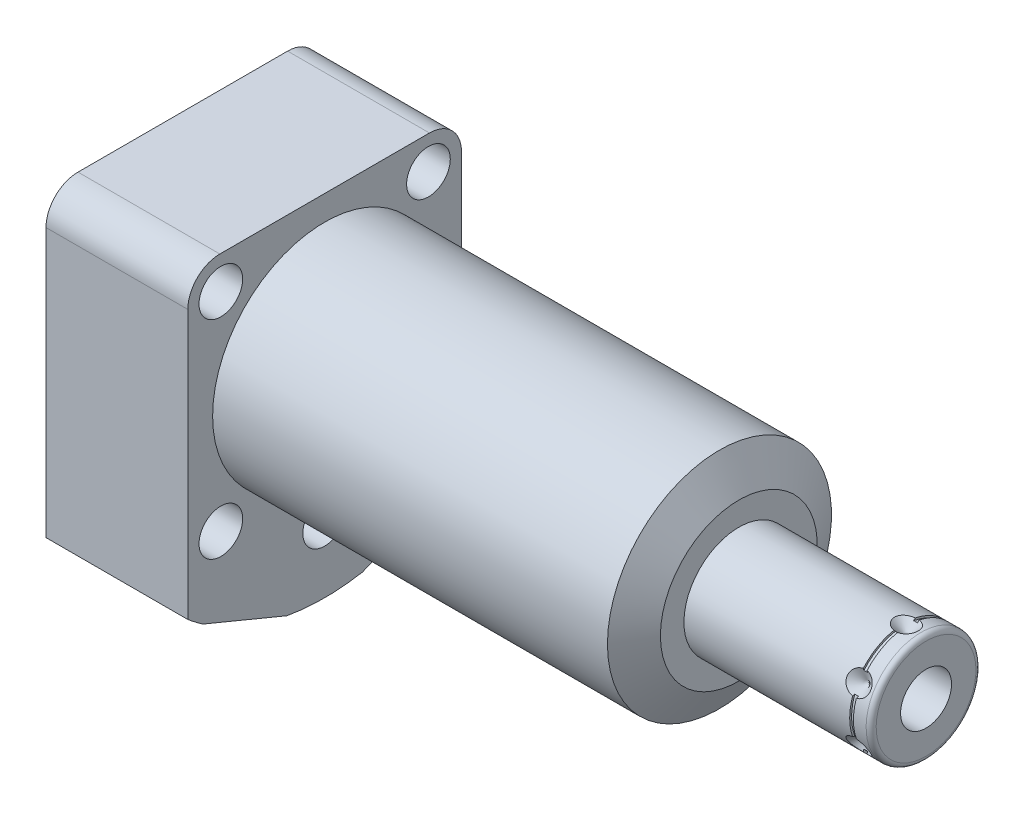
SolidWorks part; units mm, degrees
material "Alloy Steel"
ref_plane "Front Plane" through (0, 0, 0) normal (0, 0, 1) x (1, 0, 0)
ref_plane "Top Plane" through (0, 0, 0) normal (0, 1, 0) x (1, 0, 0)
ref_plane "Right Plane" through (0, 0, 0) normal (1, 0, 0) x (0, 0, -1)
sketch "Sketch1" plane through (0, 0, 0) normal (1, 0, 0) x (0, 0, -1)
  line L0 (-27.686, 27.686) -> (-27.686, -33.136)
  line L1 (-24.6412, -35.4588) -> (-7.6492, -42.4971)
  line L2 (7.6492, -42.4971) -> (24.6412, -35.4588)
  line L3 (27.686, -33.136) -> (27.686, 27.686)
  line L4 (27.686, 27.686) -> (-27.686, 27.686)
  line L5 (0, -34.1122) -> (0, 17.8562) construction
  line L6 (-36.4519, 0) -> (54.4719, 0) construction
  arc A0 (-7.6492, -42.4971) -> (7.6492, -42.4971) centre (0, 0) ccw
  arc A1 (-27.686, -33.136) -> (-24.6412, -35.4588) centre (0, 0) ccw
  arc A2 (24.6412, -35.4588) -> (27.686, -33.136) centre (0, 0) ccw
  dimension "D6" = 43.18
  dimension "D1" = 55.372
  dimension "D2" = 42.1894
  dimension "D4" = 27.686
  dimension "D5" = 22.5
extrude "Extrude1" add sketch "Sketch1" along normal blind 83.82 and the other way blind 28.702
sketch "Sketch2" plane through (0, 0, 0) normal (1, 0, 0) x (0, 0, -1)
  line L6 (27.686, 27.686) -> (-27.686, 27.686)
  line L7 (-27.686, 27.686) -> (-27.686, -33.136)
  line L8 (-24.6412, -35.4588) -> (-7.6492, -42.4971)
  line L9 (7.6492, -42.4971) -> (24.6412, -35.4588)
  line L10 (27.686, -33.136) -> (27.686, 27.686)
  line L11 (27.686, 27.686) -> (-27.686, 27.686)
  line L12 (-27.686, 27.686) -> (-27.686, -33.136)
  line L13 (-24.6412, -35.4588) -> (-7.6492, -42.4971)
  line L14 (7.6492, -42.4971) -> (24.6412, -35.4588)
  line L15 (27.686, -33.136) -> (27.686, 27.686)
  circle A0 centre (0, 0) radius 22.6695
  arc A4 (-27.686, -33.136) -> (-24.6412, -35.4588) centre (0, 0) ccw
  arc A5 (-7.6492, -42.4971) -> (7.6492, -42.4971) centre (0, 0) ccw
  arc A6 (24.6412, -35.4588) -> (27.686, -33.136) centre (0, 0) ccw
  arc A7 (-27.686, -33.136) -> (-24.6412, -35.4588) centre (0, 0) ccw
  arc A8 (-7.6492, -42.4971) -> (7.6492, -42.4971) centre (0, 0) ccw
  arc A9 (24.6412, -35.4588) -> (27.686, -33.136) centre (0, 0) ccw
  dimension "D2" = 45.339
  dimension "D1" = 0
extrude "Cut-Extrude1" cut sketch "Sketch2" along normal up to next
sketch "Sketch3" plane through (0, 0, 0) normal (0, 0, 1) x (1, 0, 0)
  line L0 (79.8972, 22.6695) -> (83.82, 15.875)
  line L1 (23.3045, 0) -> (44.9603, 0) construction
  line L2 (83.82, 22.6695) -> (83.82, 15.875)
  line L3 (83.82, 22.6695) -> (79.8972, 22.6695)
  line L4 (83.82, -22.6695) -> (83.82, 22.6695) construction
  line L5 (83.82, 22.6695) -> (0, 22.6695) construction
  dimension "D1" = 30
  dimension "D2" = 31.75
revolve "Cut-Revolve1" cut sketch "Sketch3" angle 360 about L1
ref_plane "Plane19" through (0, 0, 11.8618) normal (0, 0, 1) x (1, 0, 0)
sketch "S2D0002" plane through (-24.9936, -18.1864, 11.8618) normal (0, 0, 1) x (0, 1, 0)
  line L0 (-7.1374, 2.2606) -> (-4.6863, 2.2606)
  line L1 (-7.1374, 2.2606) -> (-7.1374, -0.7366)
  line L2 (-7.1374, -0.7366) -> (-9.144, -0.7366)
  line L3 (-9.144, -0.7366) -> (-9.144, -9.7282)
  line L4 (-9.144, -9.7282) -> (-10.3886, -9.7282)
  line L5 (-10.3886, -9.7282) -> (-10.3886, 3.7084)
  line L6 (-10.3886, -23.5585) -> (-10.3886, 0.5994) construction
  line L7 (-4.6863, 2.2606) -> (-4.6863, 3.7084)
  line L8 (45.8724, 3.7084) -> (-14.9496, 3.7084) construction
  line L9 (-4.6863, 3.7084) -> (-10.3886, 3.7084)
  dimension "D1" = 1.4478
  dimension "D2" = 28.575
  dimension "D3" = 11.4046
  dimension "D4" = 6.5024
  dimension "D5" = 2.4892
  dimension "D6" = 8.9916
  dimension "D7" = 2.9972
revolve "Cut-Revolve2" cut sketch "S2D0002" angle 360 about L6
ref_plane "Plane20" through (-12.192, 0, 0) normal (1, 0, 0) x (0, 0, -1)
sketch "Sketch6" plane through (-12.192, 0, 0) normal (1, 0, 0) x (0, 0, -1)
  line L0 (-22.1962, -36.1966) -> (-25.9797, -34.6294)
  line L1 (-22.1962, -36.1966) -> (-22.1476, -36.0792)
  line L2 (-22.1476, -36.0792) -> (-21.2184, -35.6943)
  line L3 (-21.2184, -35.6943) -> (-16.1153, -23.3744)
  line L4 (-16.1153, -23.3744) -> (-10.6241, -25.6489)
  line L5 (-10.6241, -25.6489) -> (-16.1452, -38.9779)
  line L6 (-4.9702, -11.9991) -> (2.3899, 5.7696) construction
  line L7 (-25.9797, -34.6294) -> (-26.0769, -34.8641)
  line L8 (-24.6412, -35.4588) -> (-7.6492, -42.4971) construction
  line L9 (-26.0769, -34.8641) -> (-16.1452, -38.9779)
  line L10 (-24.6412, -35.4588) -> (-7.6492, -42.4971) construction
  dimension "D1" = 0.254
  dimension "D2" = 21.5
  dimension "D3" = 45
  dimension "D5" = 13.3096
  dimension "D6" = 11.8872
  dimension "D7" = 14.1732
  dimension "D8" = 0.127
revolve "Cut-Revolve4" cut sketch "Sketch6" angle 360 about L6
mirror "Mirror1" about plane through (0, 0, 0) normal (0, 0, 1) of "Cut-Revolve2", "Cut-Revolve4"
sketch "Sketch7" plane through (0, 0, 0) normal (0, 0, 1) x (1, 0, 0)
  line L0 (83.82, 0) -> (83.82, 11.1125)
  line L1 (83.82, 11.1125) -> (120.688, 11.1125)
  line L2 (121.704, 10.0965) -> (121.704, 0)
  line L3 (121.704, 0) -> (83.82, 0)
  line L4 (4.9931, 0) -> (66.1154, 0) construction
  line L5 (83.82, -15.875) -> (83.82, 15.875) construction
  line L6 (-28.702, 27.686) -> (-28.702, -33.136) construction
  arc A0 (121.704, 10.0965) -> (120.688, 11.1125) centre (120.688, 10.0965) ccw
  point P0 (83.82, 0)
  dimension "D3" = 1.016
  dimension "D1" = 150.406
  dimension "D2" = 22.225
revolve "Revolve1" add sketch "Sketch7" angle 360 about L4
sketch "S2D0001" plane through (0, 0, 0) normal (0, 0, 1) x (1, 0, 0)
  line L0 (121.704, -5.1562) -> (104.686, -5.1562)
  line L1 (104.686, -5.1562) -> (101.5878, 0)
  line L2 (121.704, -5.1562) -> (121.704, 0)
  line L3 (121.704, 0) -> (101.5878, 0)
  line L4 (-2.5273, 0) -> (-28.8062, 0) construction
  line L5 (121.704, -10.0965) -> (121.704, 10.0965) construction
  dimension "D1" = 10.3124
  dimension "D2" = 17.018
  dimension "D3" = 59
revolve "Cut-Revolve8" cut sketch "S2D0001" angle 360 about L4
sketch "Sketch9" plane through (0, 0, 0) normal (0, 0, 1) x (1, 0, 0)
  line L0 (117.7416, -11.1125) -> (115.3286, -11.1125)
  line L1 (115.3286, -11.1125) -> (117.7416, -8.6995)
  line L2 (117.7416, -11.1125) -> (117.7416, -8.6995)
  line L3 (117.7416, -6.2534) -> (117.7416, 0.0794) construction
  line L4 (83.82, -11.1125) -> (120.688, -11.1125) construction
  line L5 (121.704, -10.0965) -> (121.704, 10.0965) construction
  dimension "D1" = 3.9624
  dimension "D2" = 45
  dimension "D3" = 4.826
revolve "Cut-Revolve9" cut sketch "Sketch9" angle 360 about L3
sketch "Sketch11" plane through (0, 0, 0) normal (0, 1, 0) x (1, 0, 0)
  line L0 (118.1226, -11.1125) -> (118.1226, -10.7315)
  line L1 (118.1226, -10.7315) -> (117.3606, -10.7315)
  line L2 (117.3606, -10.7315) -> (117.3606, -11.1125)
  line L3 (117.3606, -11.1125) -> (118.1226, -11.1125)
  line L4 (0, 0) -> (83.4312, 0) construction
  line L6 (83.82, -11.1125) -> (120.688, -11.1125) construction
  line L7 (117.7416, 0) -> (117.7416, -20.2865) construction
  dimension "D1" = 0.762
  dimension "D2" = 0.381
revolve "Cut-Revolve5" cut sketch "Sketch11" angle 360 about L4
sketch "Sketch15" plane through (-24.257, 0, 0) normal (-1, 0, 0) x (0, 0, 1)
  circle A0 centre (11.8618, -28.575) radius 2.7432
  circle A1 centre (11.8618, -28.575) radius 3.2512 construction
  dimension "D1" = 5.4864
extrude "Extrude3" add sketch "Sketch15" along normal blind 2.9972
sketch "Sketch16" plane through (-27.2542, 0, 0) normal (-1, 0, 0) x (0, 0, 1)
  line L7 (13.2989, -28.575) -> (12.5804, -27.3304)
  line L8 (12.5804, -27.3304) -> (11.1432, -27.3304)
  line L9 (11.1432, -27.3304) -> (10.4247, -28.575)
  line L10 (10.4247, -28.575) -> (11.1432, -29.8196)
  line L11 (11.1432, -29.8196) -> (12.5804, -29.8196)
  line L12 (12.5804, -29.8196) -> (13.2989, -28.575)
  circle A0 centre (11.8618, -28.575) radius 1.2446 construction
  dimension "D1" = 2.4892
extrude "Cut-Extrude2" cut sketch "Sketch16" against normal blind 2.54
chamfer "Chamfer1" distance 0.381 angle 45 1 edges at (-27.2542, -28.575, 14.605)
mirror "Mirror2" about plane through (0, 0, 0) normal (0, 0, 1) of "Extrude3", "Cut-Extrude2", "Chamfer1"
sketch "Sketch21" plane through (0, 0, 11.8618) normal (0, 0, 1) x (1, 0, 0)
  line L0 (-35.9744, -28.575) -> (-17.6399, -28.575) construction
  line L3 (-27.2542, -22.8727) -> (-27.2542, -34.2773) construction
  line L4 (-24.257, -28.575) -> (-18.0186, -28.575) construction
  circle A0 centre (-28.1178, -23.7617) radius 0.889
  dimension "D1" = 1.778
  dimension "D2" = 9.6266
  dimension "D3" = 0.8636
revolve "Revolve4" add sketch "Sketch21" angle 360 about L0
mirror "Mirror3" about plane through (0, 0, 0) normal (0, 0, 1) of bodies 129
fillet "Fillet1" radius 6.477 2 edges at (-14.351, 27.686, 27.686) (-14.351, 27.686, -27.686)
hole_wizard "Hole1" positions "Sketch23" profile "Sketch22" legacy end condition up to next
sketch "Sketch23" plane through (0, 0, 0) normal (1, 0, 0) x (0, 0, -1)
  line L0 (0, 0) -> (0, 19.8912) construction
  point P0 (0, -29.6926)
  point P5 (-21.0058, 21.0058)
  point P13 (21.0058, 21.0058)
  point P14 (-21.0058, -21.0058)
  point P18 (21.0058, -21.0058)
  dimension "D1" = 29.6926
  dimension "D2" = 21.0058
  dimension "D3" = 21.0058
  dimension "D4" = 21.0058
sketch "Sketch22" plane through (0, -29.6926, 0) normal (0, 1, 0) x (0, 0, -1)
  line L0 (0, 0) -> (0, 28.702)
  line L1 (0, 28.702) -> (4.4196, 28.702)
  line L2 (4.4196, 28.702) -> (4.4196, 0)
  line L3 (4.4196, 0) -> (0, 0)
  line L4 (0, 110) -> (0, -10) construction
  dimension "Diameter" = 8.8392
  dimension "Depth" = 28.702
pattern_circular "CirPattern1" count 6 over 360 about axis through (83.821, 0, 0) along (-1, 0, 0) of "Cut-Revolve9"
